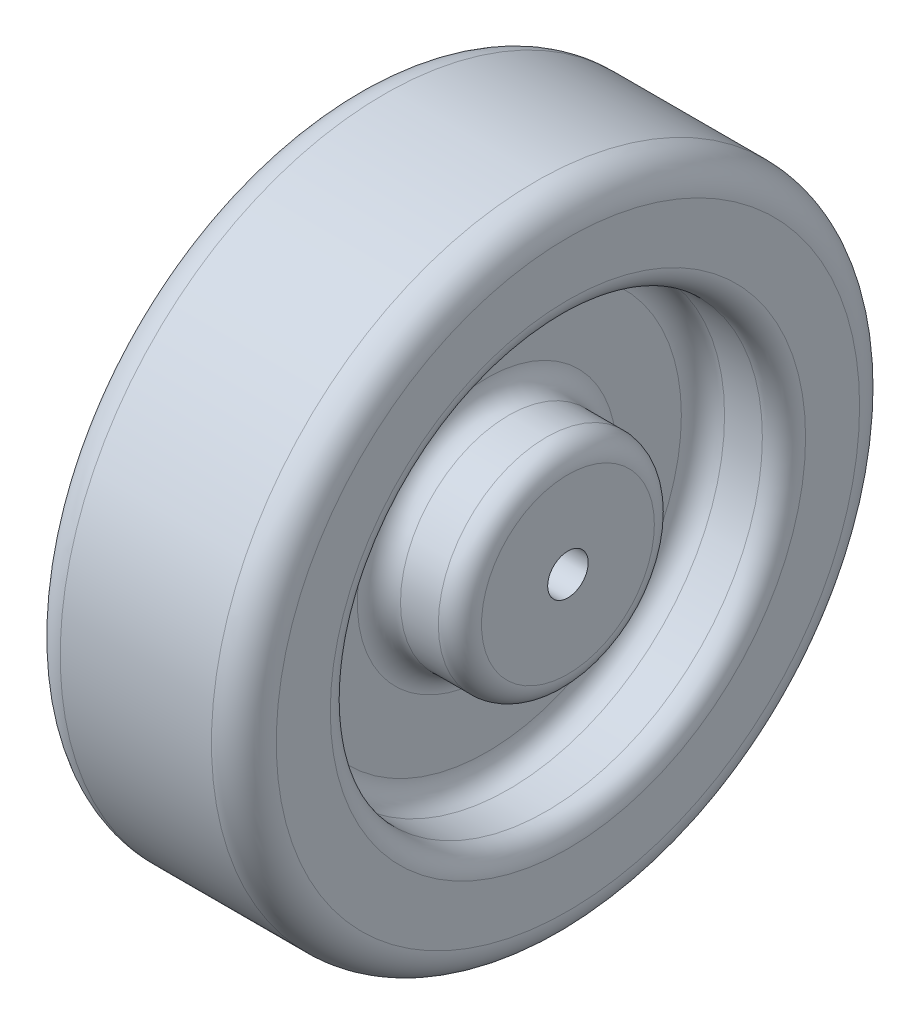
SolidWorks part; units mm, degrees
ref_plane "Front Plane" through (0, 0, 0) normal (0, 0, 1) x (1, 0, 0)
ref_plane "Top Plane" through (0, 0, 0) normal (0, 1, 0) x (1, 0, 0)
ref_plane "Right Plane" through (0, 0, 0) normal (1, 0, 0) x (0, 0, -1)
sketch "Sketch1" plane through (0, 0, 0) normal (1, 0, 0) x (0, 0, -1)
  circle A0 centre (0, 0) radius 76.2
  dimension "D1" = 152.4
extrude "Boss-Extrude1" add sketch "Sketch1" along normal blind 50.8
sketch "Sketch2" plane through (50.8, 0, 0) normal (1, 0, 0) x (0, 0, -1)
  circle A0 centre (0, 0) radius 50.8
  circle A1 centre (0, 0) radius 25.4
  dimension "D1" = 101.6
  dimension "D2" = 50.8
extrude "Cut-Extrude1" cut sketch "Sketch2" against normal blind 19.05
sketch "Sketch3" plane through (0, 0, 0) normal (-1, 0, 0) x (0, 0, 1)
  circle A0 centre (0, 0) radius 25.4
  circle A1 centre (0, 0) radius 50.8
  dimension "D1" = 101.6
  dimension "D2" = 50.8
extrude "Cut-Extrude2" cut sketch "Sketch3" against normal blind 19.05
sketch "Sketch4" plane through (0, 0, 0) normal (-1, 0, 0) x (0, 0, 1)
  circle A0 centre (0, 0) radius 4.7625
  dimension "D1" = 9.525
extrude "Cut-Extrude3" cut sketch "Sketch4" against normal through all
fillet "Fillet1" radius 7.62 2 edges at (0, 0, -76.2) (50.8, 0, -76.2)
fillet "Fillet2" radius 5.08 8 edges at (31.75, 0, -25.4) (31.75, 0, -50.8) (50.8, 0, -50.8) (50.8, 0, -25.4) (19.05, 0, 25.4) (0, 0, 50.8) (19.05, 0, 50.8) (0, 0, 25.4)
